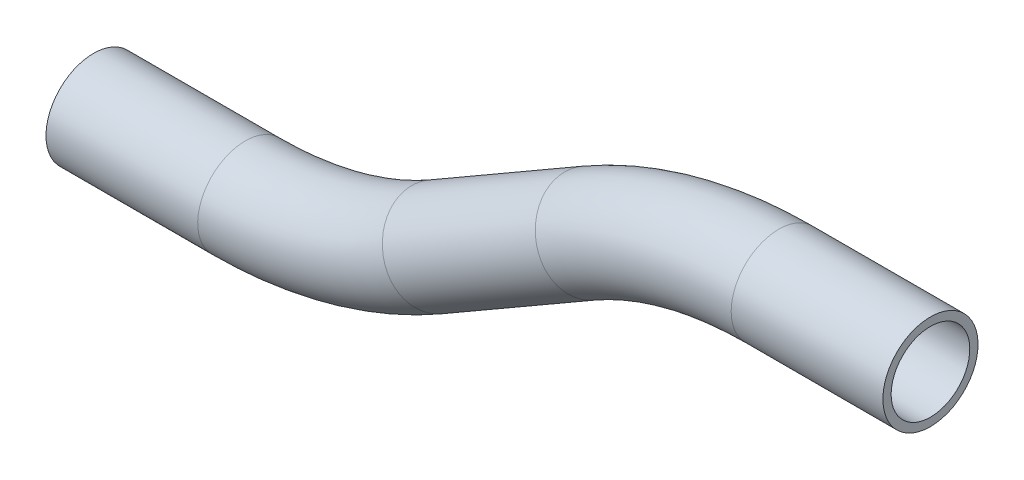
SolidWorks part; units mm, degrees
material "6061 Alloy"
ref_plane "Front Plane" through (0, 0, 0) normal (0, 0, 1) x (1, 0, 0)
ref_plane "Top Plane" through (0, 0, 0) normal (0, 1, 0) x (1, 0, 0)
ref_plane "Right Plane" through (0, 0, 0) normal (1, 0, 0) x (0, 0, -1)
sketch "Sketch1" plane through (0, 0, 0) normal (0, 0, 1) x (1, 0, 0)
  line L0 (0, 0) -> (30.3823, 0)
  line L2 (-38.1, -10.2089) -> (-68.7266, -27.8911)
  line L3 (-68.7266, -27.8911) -> (-20.4177, 0)
  line L4 (30.3823, 0) -> (-20.4177, 0)
  line L5 (-106.8266, -38.1) -> (-137.2089, -38.1)
  line L6 (-137.2089, -38.1) -> (-86.4089, -38.1)
  line L7 (-38.1, -10.2089) -> (-86.4089, -38.1)
  arc A0 (0, 0) -> (-38.1, -10.2089) centre (0, -76.2) ccw
  arc A1 (-68.7266, -27.8911) -> (-106.8266, -38.1) centre (-106.8266, 38.1) cw
  point P9 (-20.4177, 0)
  point P14 (-86.4089, -38.1)
  dimension "D3" = 30
  dimension "D4" = 30
  dimension "D1" = 76.2
  dimension "D2" = 76.2
  dimension "D5" = 76.2
  dimension "D6" = 50.8
  dimension "D7" = 50.8
ref_plane "Plane1" through (30.3823, 0, 0) normal (-1, 0, 0) x (0, 0, 1)
sketch "Sketch2" plane through (30.3823, 0, 0) normal (-1, 0, 0) x (0, 0, 1)
  circle A0 centre (0, 0) radius 9.525
  circle A1 centre (0, 0) radius 7.874
  dimension "D1" = 19.05
  dimension "D2" = 15.748
sweep "Sweep1" add profiles "Sketch2" path "Sketch1"
